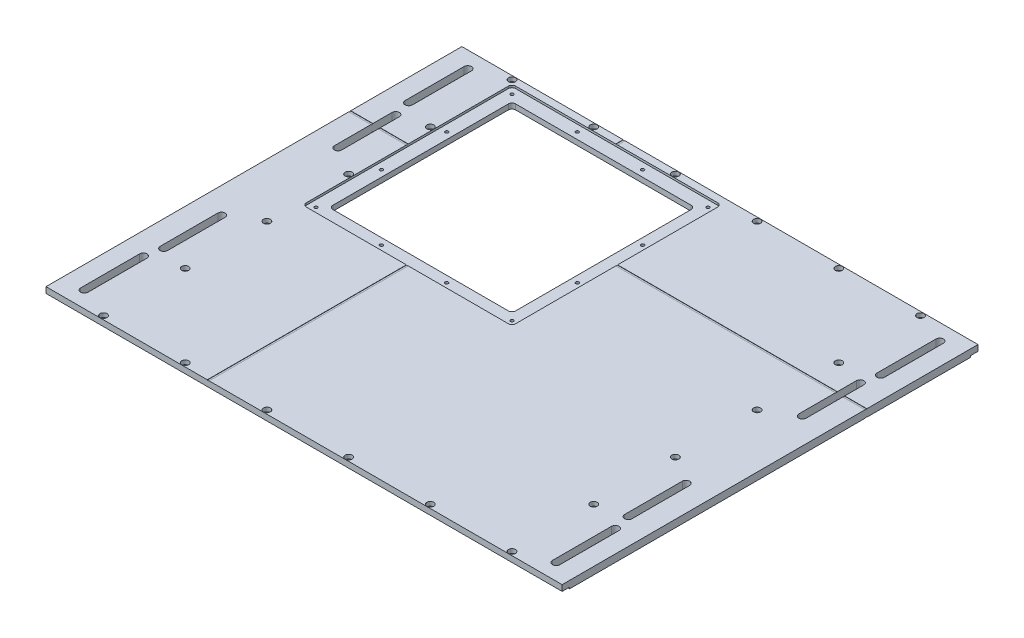
SolidWorks part; units mm, degrees
material "6061 Alloy"
ref_plane "Front Plane" through (0, 0, 0) normal (0, 0, 1) x (1, 0, 0)
ref_plane "Top Plane" through (0, 0, 0) normal (0, 1, 0) x (1, 0, 0)
ref_plane "Right Plane" through (0, 0, 0) normal (1, 0, 0) x (0, 0, -1)
sketch "Sketch1" plane through (0, 0, 0) normal (0, 1, 0) x (1, 0, 0)
  line L1 (0, 0) -> (444.5, 0)
  line L2 (0, 0) -> (0, 358.14)
  line L3 (0, 358.14) -> (444.5, 358.14)
  line L4 (444.5, 0) -> (444.5, 358.14)
  dimension "D1" = 444.5
  dimension "D2" = 358.14
extrude "Boss-Extrude1" add sketch "Sketch1" along normal blind 6.35
sketch "Sketch2" plane through (0, 6.35, 0) normal (0, 1, 0) x (1, 0, 0)
  line L1 (64.135, 182.88) -> (215.265, 182.88)
  line L2 (60.96, 186.055) -> (60.96, 337.185)
  line L3 (64.135, 340.36) -> (215.265, 340.36)
  line L4 (218.44, 186.055) -> (218.44, 337.185)
  line L6 (222.25, 358.14) -> (222.25, 0) construction
  line L7 (444.5, 358.14) -> (0, 358.14) construction
  line L8 (0, 0) -> (444.5, 0) construction
  line L9 (444.5, 179.07) -> (0, 179.07) construction
  line L10 (444.5, 0) -> (444.5, 358.14) construction
  line L11 (0, 358.14) -> (0, 0) construction
  arc A0 (64.135, 182.88) -> (60.96, 186.055) centre (64.135, 186.055) cw
  arc A1 (215.265, 182.88) -> (218.44, 186.055) centre (215.265, 186.055) ccw
  arc A2 (215.265, 340.36) -> (218.44, 337.185) centre (215.265, 337.185) cw
  arc A3 (60.96, 337.185) -> (64.135, 340.36) centre (64.135, 337.185) cw
  point P18 (60.96, 182.88)
  point P23 (218.44, 340.36)
  point P26 (60.96, 340.36)
  dimension "D5" = 3.175
  dimension "D1" = 157.48
  dimension "D2" = 157.48
  dimension "D3" = 3.81
  dimension "D4" = 3.81
extrude "Cut-Extrude1" cut sketch "Sketch2" against normal blind 6.35
sketch "Sketch3" plane through (0, 6.35, 0) normal (0, 1, 0) x (1, 0, 0)
  line L0 (64.135, 182.88) -> (215.265, 182.88) construction
  line L1 (52.705, 171.45) -> (226.695, 171.45)
  line L2 (49.53, 174.625) -> (49.53, 348.615)
  line L3 (52.705, 351.79) -> (226.695, 351.79)
  line L4 (229.87, 174.625) -> (229.87, 348.615)
  line L8 (218.44, 186.055) -> (218.44, 337.185) construction
  arc A0 (52.705, 351.79) -> (49.53, 348.615) centre (52.705, 348.615) ccw
  arc A1 (49.53, 174.625) -> (52.705, 171.45) centre (52.705, 174.625) ccw
  arc A2 (226.695, 171.45) -> (229.87, 174.625) centre (226.695, 174.625) ccw
  arc A3 (229.87, 348.615) -> (226.695, 351.79) centre (226.695, 348.615) ccw
  point P10 (49.53, 351.79)
  point P13 (49.53, 171.45)
  point P16 (229.87, 171.45)
  dimension "D5" = 3.175
  dimension "D1" = 180.34
  dimension "D2" = 180.34
  dimension "D3" = 11.43
  dimension "D4" = 11.43
extrude "Cut-Extrude2" cut sketch "Sketch3" against normal blind 1.8542
hole_wizard "CBORE for #6 Socket Head Cap Screw1" positions "Sketch10" profile "Sketch8" counterbore size "#6" standard "ANSI Inch" end condition through all
sketch "Sketch10" plane through (0, 6.35, 0) normal (0, 1, 0) x (1, 0, 0)
  line L0 (444.5, 358.14) -> (0, 358.14) construction
  line L2 (222.25, 358.14) -> (222.25, 304.2515) construction
  line L4 (353.1684, 309.9884) -> (222.25, 179.07) construction
  line L6 (444.5, 179.07) -> (263.845, 179.07) construction
  line L7 (444.5, 0) -> (444.5, 358.14) construction
  line L8 (0, 179.07) -> (444.5, 179.07) construction
  line L9 (0, 358.14) -> (0, 0) construction
  line L10 (222.25, 0) -> (222.25, 358.14) construction
  line L11 (0, 0) -> (444.5, 0) construction
  point P0 (46.355, 354.965)
  point P12 (116.713, 354.965)
  point P14 (187.071, 354.965)
  point P31 (398.145, 354.965)
  point P32 (327.787, 354.965)
  point P33 (257.429, 354.965)
  point P34 (398.145, 3.175)
  point P35 (327.787, 3.175)
  point P36 (257.429, 3.175)
  point P37 (187.071, 3.175)
  point P38 (116.713, 3.175)
  point P39 (46.355, 3.175)
  point P40 (398.145, 284.607)
  point P41 (398.145, 214.249)
  point P42 (398.145, 143.891)
  point P43 (398.145, 73.533)
  point P44 (46.355, 73.533)
  point P45 (46.355, 143.891)
  point P46 (46.355, 214.249)
  point P47 (46.355, 284.607)
  dimension "D1" = 3.175
  dimension "D2" = 70.358
  dimension "D3" = 35.179
  dimension "D4" = 70.358
  dimension "D5" = 45
sketch "Sketch8" plane through (46.355, 6.35, -354.965) normal (1, 0, 0) x (0, 0, 1)
  line L0 (0, 0) -> (0, 6.35)
  line L1 (0, 6.35) -> (1.8288, 6.35)
  line L3 (1.8288, 6.35) -> (1.8288, 3.5052)
  line L4 (1.8288, 3.5052) -> (3, 3.5052)
  line L5 (3, 3.5052) -> (3, 0)
  line L7 (3, 0) -> (0, 0)
  line L11 (0, -6.35) -> (0, 107.95) construction
  dimension "Thru Hole Dia." = 3.6576
  dimension "Thru Hole Depth" = 6.35
  dimension "C'Bore Dia." = 6
  dimension "C'Bore Depth" = 3.5052
hole_wizard "CBORE for #6 Socket Head Cap Screw2" positions "Sketch15" profile "Sketch16" counterbore size "#6" standard "ANSI Inch"
sketch "Sketch15" plane through (249.4625, 6.35, -88.9524) normal (0, 1, 0) x (0, 0, 1)
  line L0 (88.9524, -27.2125) -> (-269.1876, -27.2125) construction
  line L1 (88.9524, -249.4625) -> (88.9524, 195.0375) construction
  line L2 (-269.1876, 195.0375) -> (-269.1876, -249.4625) construction
  line L3 (-269.1876, -27.2125) -> (-90.1176, 195.0375) construction
  line L4 (88.9524, 195.0375) -> (-269.1876, 195.0375) construction
  line L5 (-90.1176, 195.0375) -> (-90.1176, -249.4625) construction
  line L6 (-269.1876, -249.4625) -> (88.9524, -249.4625) construction
  line L7 (-90.1176, -249.4625) -> (88.9524, -27.2125) construction
  point P0 (-90.1176, 55.3375)
  point P3 (-172.6676, -27.2125)
  point P6 (-255.2176, -192.3125)
  point P9 (74.9824, 137.8875)
  point P12 (-172.6676, 137.8875)
  point P15 (-255.2176, 55.3375)
  dimension "D1" = 82.55
  dimension "D2" = 82.55
  dimension "D3" = 165.1
  dimension "D4" = 165.1
  dimension "D5" = 82.55
  dimension "D6" = 82.55
  dimension "D7" = 165.1
  dimension "D8" = 165.1
  dimension "D9" = 165.1
  dimension "D10" = 165.1
sketch "Sketch16" plane through (304.8, 6.35, -179.07) normal (1, 0, 0) x (0, 0, 1)
  line L0 (0, 0) -> (0, 6.35)
  line L1 (0, 6.35) -> (1.8288, 6.35)
  line L3 (1.8288, 6.35) -> (1.8288, 3.5052)
  line L4 (1.8288, 3.5052) -> (3, 3.5052)
  line L5 (3, 3.5052) -> (3, 0)
  line L7 (3, 0) -> (0, 0)
  line L11 (0, -6.35) -> (0, 107.95) construction
  dimension "Thru Hole Dia." = 3.6576
  dimension "Thru Hole Depth" = 6.35
  dimension "C'Bore Dia." = 6
  dimension "C'Bore Depth" = 3.5052
hole_wizard "Tap Drill for #6-32 Tap1" positions "Sketch17" profile "Sketch18" hole size "#6-32" standard "ANSI Inch"
sketch "Sketch17" plane through (249.4625, 4.4958, -88.9524) normal (0, 1, 0) x (0, 0, 1)
  line L11 (-262.8376, -194.154) -> (-82.4976, -194.154) construction
  line L12 (-262.8376, -22.7675) -> (-262.8376, -196.7575) construction
  line L13 (-82.4976, -196.7575) -> (-82.4976, -22.7675) construction
  line L17 (-257.0591, -19.5925) -> (-257.0591, -199.9325) construction
  line L22 (-88.2761, -19.5925) -> (-88.2761, -199.9325) construction
  line L23 (-85.6726, -19.5925) -> (-259.6626, -19.5925) construction
  line L24 (-259.6626, -199.9325) -> (-85.6726, -199.9325) construction
  line L28 (-259.6626, -199.9325) -> (-85.6726, -199.9325) construction
  line L29 (-85.6726, -19.5925) -> (-259.6626, -19.5925) construction
  line L30 (-262.8376, -22.7675) -> (-262.8376, -196.7575) construction
  line L31 (-262.8376, -109.7625) -> (-82.4976, -109.7625) construction
  line L35 (-172.6676, -199.9325) -> (-172.6676, -19.5925) construction
  point P121 (-257.0591, -194.154)
  point P123 (-88.2761, -194.154)
  point P125 (-144.5371, -194.154)
  point P127 (-200.7981, -194.154)
  point P129 (-257.0591, -137.893)
  point P131 (-88.2761, -137.893)
  point P162 (-88.2761, -81.632)
  point P163 (-88.2761, -25.371)
  point P164 (-144.5371, -25.371)
  point P165 (-200.7981, -25.371)
  point P166 (-257.0591, -25.371)
  point P167 (-257.0591, -81.632)
  dimension "D1" = 28.1305
  dimension "D2" = 28.1305
  dimension "D3" = 28.1305
  dimension "D4" = 56.261
  dimension "D5" = 56.261
  dimension "D6" = 56.261
  dimension "D7" = 56.261
sketch "Sketch18" plane through (55.3085, 4.4958, -346.0115) normal (1, 0, 0) x (0, 0, 1)
  line L0 (0, 0) -> (0, 5.3075)
  line L1 (0, 5.3075) -> (1.3525, 4.4948)
  line L2 (1.3525, 4.4948) -> (1.3525, 0)
  line L3 (1.3525, 0) -> (0, 0)
  line L4 (0, 5.3075) -> (-1.3526, 4.4948) construction
  line L5 (0, -6.35) -> (0, 107.95) construction
  dimension "Hole Dia." = 2.7051
  dimension "Hole Depth" = 4.4948
  dimension "Drill Angle" = 118
sketch "Sketch21" plane through (0, 0, 0) normal (0, -1, 0) x (1, 0, 0)
  line L0 (444.5, -358.14) -> (444.5, -351.79)
  line L1 (0, -358.14) -> (444.5, -358.14)
  line L2 (43.18, -6.35) -> (43.18, -351.79)
  line L3 (401.32, -6.35) -> (444.5, -6.35)
  line L4 (401.32, -6.35) -> (401.32, -351.79)
  line L6 (49.53, -6.35) -> (49.53, -351.79)
  line L7 (49.53, -351.79) -> (394.97, -351.79)
  line L8 (394.97, -6.35) -> (394.97, -351.79)
  line L9 (49.53, -6.35) -> (394.97, -6.35)
  line L10 (0, -358.14) -> (0, 0) construction
  line L11 (444.5, 0) -> (444.5, -358.14) construction
  line L12 (401.32, -351.79) -> (444.5, -351.79)
  line L14 (444.5, 0) -> (0, 0)
  line L15 (43.18, -351.79) -> (0, -351.79)
  line L16 (0, -351.79) -> (0, -358.14)
  line L17 (222.25, 0) -> (222.25, -358.14) construction
  line L18 (43.18, 0) -> (43.18, -358.14) construction
  line L19 (401.32, 0) -> (401.32, -358.14) construction
  line L20 (43.18, -6.35) -> (0, -6.35)
  line L21 (0, -6.35) -> (0, 0)
  line L24 (444.5, -6.35) -> (444.5, 0)
  line L26 (43.18, 0) -> (401.32, 0) construction
  line L27 (43.18, -358.14) -> (401.32, -358.14) construction
  dimension "D1" = 6.35
  dimension "D2" = 179.07
  dimension "D3" = 179.07
  dimension "D4" = 6.35
  dimension "D5" = 6.35
extrude "Cut-Extrude3" cut sketch "Sketch21" against normal blind 1.27
sketch "Sketch22" plane through (0, 0, 0) normal (0, -1, 0) x (1, 0, 0)
  line L0 (0, -179.07) -> (444.5, -179.07) construction
  line L1 (0, -351.79) -> (0, -6.35) construction
  line L2 (444.5, -6.35) -> (444.5, -351.79) construction
  line L3 (19.05, -17.8024) -> (19.05, -325.294) construction
  line L4 (444.5, 0) -> (0, 0) construction
  line L5 (222.25, 0) -> (222.25, -179.07) construction
  line L6 (222.25, -179.07) -> (222.25, -358.14) construction
  line L7 (0, -358.14) -> (444.5, -358.14) construction
  line L8 (422.25, -28.721) -> (422.25, -337.5933) construction
  line L9 (19.05, -13.97) -> (19.05, -64.77) construction
  line L10 (422.25, -79.2415) -> (422.25, -128.8985) construction
  line L11 (22.2504, -13.97) -> (22.2504, -64.77)
  line L12 (15.8496, -13.97) -> (15.8496, -64.77)
  line L13 (19.05, -344.17) -> (19.05, -293.37) construction
  line L14 (425.425, -79.2415) -> (425.425, -128.8985)
  line L15 (419.075, -79.2415) -> (419.075, -128.8985)
  line L16 (22.2504, -344.17) -> (22.2504, -293.37)
  line L17 (15.8496, -344.17) -> (15.8496, -293.37)
  line L18 (425.45, -13.97) -> (425.45, -64.77) construction
  line L19 (422.2496, -13.97) -> (422.2496, -64.77)
  line L20 (428.6504, -13.97) -> (428.6504, -64.77)
  line L21 (425.45, -344.17) -> (425.45, -293.37) construction
  line L22 (422.2496, -344.17) -> (422.2496, -293.37)
  line L23 (428.6504, -344.17) -> (428.6504, -293.37)
  line L24 (22.25, -79.2415) -> (22.25, -128.8985) construction
  line L25 (19.075, -79.2415) -> (19.075, -128.8985)
  line L26 (25.425, -79.2415) -> (25.425, -128.8985)
  line L27 (22.25, -278.8985) -> (22.25, -229.2415) construction
  line L28 (19.075, -278.8985) -> (19.075, -229.2415)
  line L29 (25.425, -278.8985) -> (25.425, -229.2415)
  line L30 (422.25, -278.8985) -> (422.25, -229.2415) construction
  line L31 (425.425, -278.8985) -> (425.425, -229.2415)
  line L32 (419.075, -278.8985) -> (419.075, -229.2415)
  arc A0 (22.2504, -13.97) -> (15.8496, -13.97) centre (19.05, -13.97) ccw
  arc A1 (15.8496, -64.77) -> (22.2504, -64.77) centre (19.05, -64.77) ccw
  arc A2 (425.425, -79.2415) -> (419.075, -79.2415) centre (422.25, -79.2415) ccw
  arc A3 (419.075, -128.8985) -> (425.425, -128.8985) centre (422.25, -128.8985) ccw
  arc A4 (22.2504, -344.17) -> (15.8496, -344.17) centre (19.05, -344.17) cw
  arc A5 (15.8496, -293.37) -> (22.2504, -293.37) centre (19.05, -293.37) cw
  arc A6 (422.2496, -13.97) -> (428.6504, -13.97) centre (425.45, -13.97) cw
  arc A7 (428.6504, -64.77) -> (422.2496, -64.77) centre (425.45, -64.77) cw
  arc A8 (422.2496, -344.17) -> (428.6504, -344.17) centre (425.45, -344.17) ccw
  arc A9 (428.6504, -293.37) -> (422.2496, -293.37) centre (425.45, -293.37) ccw
  arc A10 (19.075, -79.2415) -> (25.425, -79.2415) centre (22.25, -79.2415) cw
  arc A11 (25.425, -128.8985) -> (19.075, -128.8985) centre (22.25, -128.8985) cw
  arc A12 (19.075, -278.8985) -> (25.425, -278.8985) centre (22.25, -278.8985) ccw
  arc A13 (25.425, -229.2415) -> (19.075, -229.2415) centre (22.25, -229.2415) ccw
  arc A14 (425.425, -278.8985) -> (419.075, -278.8985) centre (422.25, -278.8985) cw
  arc A15 (419.075, -229.2415) -> (425.425, -229.2415) centre (422.25, -229.2415) cw
  point P21 (19.05, -39.37)
  point P28 (422.25, -104.07)
  point P33 (19.05, -318.77)
  point P40 (425.45, -39.37)
  point P47 (425.45, -318.77)
  point P54 (22.25, -104.07)
  point P61 (22.25, -254.07)
  point P68 (422.25, -254.07)
  dimension "D3" = 49.657
  dimension "D7" = 75
  dimension "D1" = 203.2
  dimension "D2" = 200
  dimension "D4" = 50.8
  dimension "D5" = 139.7
  dimension "D6" = 6.35
extrude "Cut-Extrude4" cut sketch "Sketch22" against normal through all
sketch "Sketch24" plane through (0, 6.35, 0) normal (0, 1, 0) x (1, 0, 0)
  line L0 (229.87, 261.62) -> (444.5004, 261.62) construction
  line L1 (215.265, 182.88) -> (64.135, 182.88) construction
  line L2 (444.5, 358.14) -> (0, 358.14) construction
  line L3 (139.7, 358.14) -> (139.7, 351.8067) construction
  line L4 (0, 0) -> (444.5, 0) construction
  line L5 (139.7, 365.76) -> (139.7, 351.8067) construction
  line L6 (140.4937, 365.76) -> (140.4937, 351.8067)
  line L7 (138.9062, 365.76) -> (138.9062, 351.8067)
  line L8 (229.87, 174.625) -> (229.87, 348.615) construction
  line L9 (229.87, 261.62) -> (-0.0003, 261.62) construction
  line L10 (459.7403, 261.62) -> (-0.0003, 261.62) construction
  line L11 (459.7403, 260.8262) -> (-0.0003, 260.8262)
  line L12 (459.7403, 262.4137) -> (-0.0003, 262.4137)
  line L15 (138.9062, 351.8067) -> (140.4937, 351.8067)
  line L17 (138.9062, 171.45) -> (140.4937, 171.45)
  line L18 (52.705, 171.45) -> (226.695, 171.45) construction
  line L22 (140.4937, 171.45) -> (140.4938, 0)
  line L23 (139.7, 182.88) -> (139.7, 0) construction
  line L24 (139.7, 182.88) -> (139.7, 0) construction
  line L25 (138.9062, 171.45) -> (138.9063, 0)
  line L31 (139.7, 351.8067) -> (139.7, 358.14) construction
  arc A0 (140.4937, 365.76) -> (138.9062, 365.76) centre (139.7, 365.76) ccw
  arc A1 (138.9063, 0) -> (140.4938, 0) centre (139.7, 0) ccw
  arc A2 (459.7403, 260.8262) -> (459.7403, 262.4137) centre (459.7403, 261.62) ccw
  arc A3 (-0.0003, 262.4137) -> (-0.0003, 260.8262) centre (-0.0003, 261.62) ccw
  point P10 (139.7, 182.88)
  point P21 (229.87, 261.62)
  dimension "D1" = 1.5875
  dimension "D2" = 1.5875
  dimension "D3" = 1.5875
extrude "Cut-Extrude6" cut sketch "Sketch24" against normal blind 0.254
sketch "Sketch25" plane through (0, 0, 0) normal (0, -1, 0) x (1, 0, 0)
  line L0 (60.96, -261.62) -> (0, -261.62) construction
  line L1 (60.96, -337.185) -> (60.96, -186.055) construction
  line L2 (0, -351.79) -> (0, -6.35) construction
  line L3 (60.96, -261.62) -> (444.5, -261.62) construction
  line L4 (444.5, -6.35) -> (444.5, -351.79) construction
  line L5 (-38.1, -261.62) -> (38.1, -261.62) construction
  line L7 (-38.1, -260.8262) -> (38.1, -260.8262)
  line L8 (-38.1, -262.4137) -> (38.1, -262.4137)
  line L9 (482.6, -261.62) -> (406.4, -261.62) construction
  line L10 (482.6, -262.4137) -> (406.4, -262.4137)
  line L11 (482.6, -260.8262) -> (406.4, -260.8262)
  arc A0 (-38.1, -260.8262) -> (-38.1, -262.4137) centre (-38.1, -261.62) ccw
  arc A1 (38.1, -262.4137) -> (38.1, -260.8262) centre (38.1, -261.62) ccw
  arc A2 (482.6, -262.4137) -> (482.6, -260.8262) centre (482.6, -261.62) ccw
  arc A3 (406.4, -260.8262) -> (406.4, -262.4137) centre (406.4, -261.62) ccw
  point P14 (0, -261.62)
  point P21 (444.5, -261.62)
extrude "Cut-Extrude7" cut sketch "Sketch25" against normal blind 0.254
